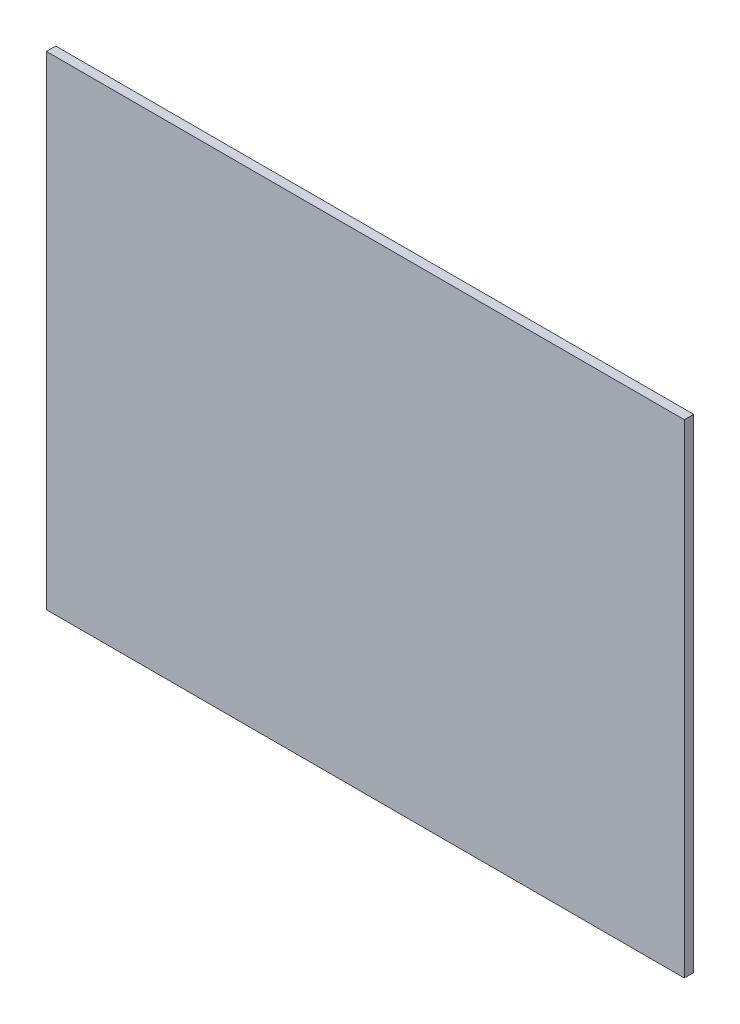
SolidWorks part; units mm, degrees
ref_plane "Plan de face" through (0, 0, 0) normal (0, 0, 1) x (1, 0, 0)
ref_plane "Plan de dessus" through (0, 0, 0) normal (0, 1, 0) x (1, 0, 0)
ref_plane "Plan de droite" through (0, 0, 0) normal (1, 0, 0) x (0, 0, -1)
sketch "Esquisse1" plane through (0, 0, 0) normal (0, 0, 1) x (1, 0, 0)
  line L1 (19.4828, -526.4004) -> (223.9828, -526.4004)
  line L2 (19.4828, -526.4004) -> (19.4828, -681.4004)
  line L3 (19.4828, -681.4004) -> (223.9828, -681.4004)
  line L4 (223.9828, -526.4004) -> (223.9828, -681.4004)
  dimension "D1" = 155
  dimension "D2" = 204.5
extrude "Boss.-Extru.1" add sketch "Esquisse1" along normal blind 3
